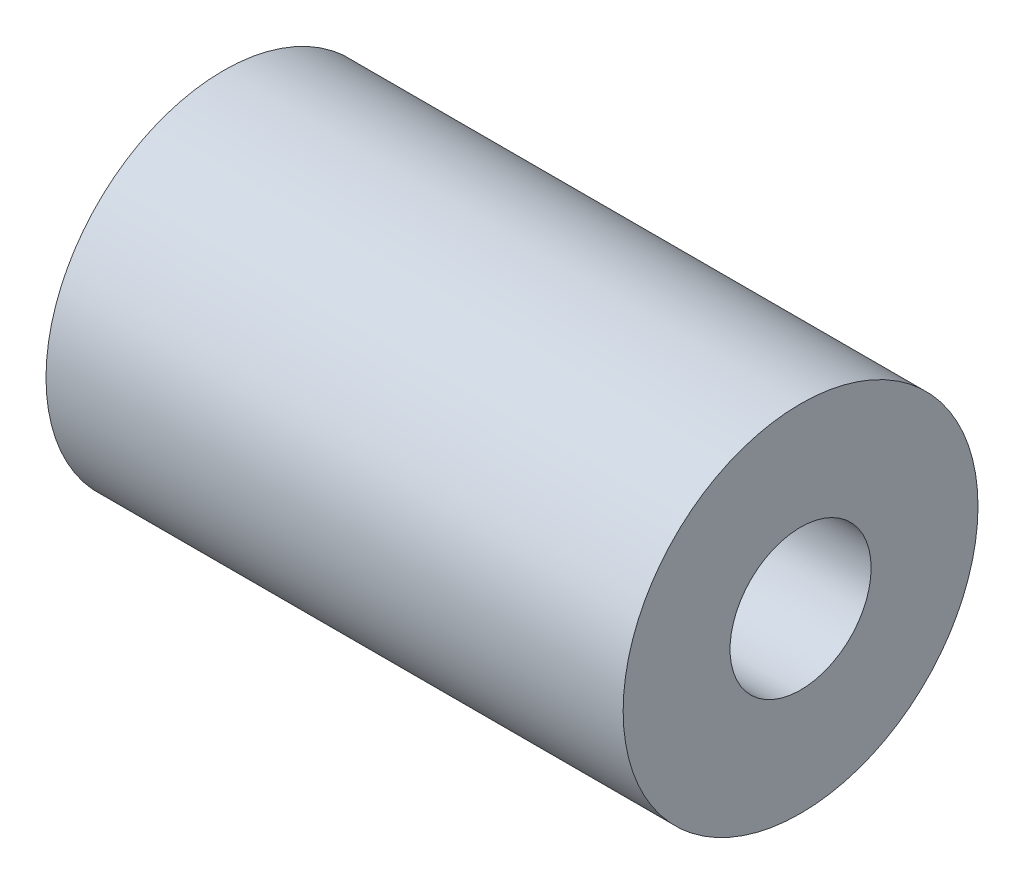
SolidWorks part; units mm, degrees
ref_plane "前视基准面" through (0, 0, 0) normal (0, 0, 1) x (1, 0, 0)
ref_plane "上视基准面" through (0, 0, 0) normal (0, 1, 0) x (1, 0, 0)
ref_plane "右视基准面" through (0, 0, 0) normal (1, 0, 0) x (0, 0, -1)
sketch "草图1" plane through (0, 0, 0) normal (1, 0, 0) x (0, 0, -1)
  circle A0 centre (0, 0) radius 1.65
  circle A1 centre (0, 0) radius 4.15
  dimension "D1" = 3.3
  dimension "D2" = 2.5
extrude "凸台-拉伸1" add sketch "草图1" along normal blind 13.5
